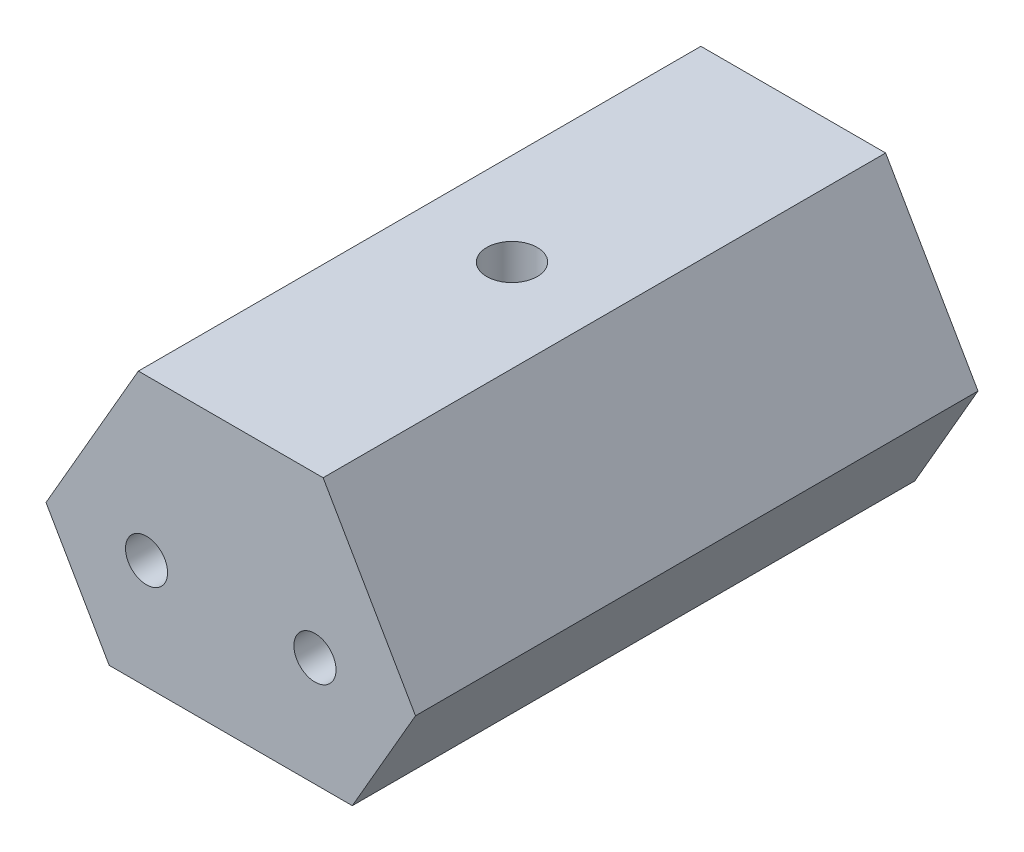
SolidWorks part; units mm, degrees
material "6061-T6 (SS)"
ref_plane "Front Plane" through (0, 0, 0) normal (0, 0, 1) x (1, 0, 0)
ref_plane "Top Plane" through (0, 0, 0) normal (0, 1, 0) x (1, 0, 0)
ref_plane "Right Plane" through (0, 0, 0) normal (1, 0, 0) x (0, 0, -1)
sketch "Sketch1" plane through (0, 0, 0) normal (0, 0, 1) x (1, 0, 0)
  line L0 (-7.2169, -6.5) -> (7.2169, -6.5)
  line L1 (-5.4848, -9.5) -> (5.4848, -9.5) construction
  line L2 (7.2169, -6.5) -> (10.9697, 0)
  line L3 (10.9697, 0) -> (5.4848, 9.5)
  line L4 (5.4848, 9.5) -> (-5.4848, 9.5)
  line L5 (-5.4848, 9.5) -> (-10.9697, 0)
  line L6 (-10.9697, 0) -> (-7.2169, -6.5)
  line L7 (-7.2169, -6.5) -> (-5.4848, -9.5) construction
  line L8 (7.2169, -6.5) -> (5.4848, -9.5) construction
  circle A0 centre (0, 0) radius 9.5 construction
  circle A1 centre (-5, 0) radius 1.25
  circle A2 centre (-5, 0) radius 1.5 construction
  circle A3 centre (5, 0) radius 1.25
  circle A4 centre (5, 0) radius 1.5 construction
  point P20 (0, 0)
  dimension "D1" = 2.5
  dimension "D2" = 3
  dimension "D3" = 2
  dimension "D6" = 3
  dimension "D4" = 19
  dimension "D5" = 10
  dimension "D7" = 3.4641
  dimension "D8" = 3.4641
extrude "Boss-Extrude1" add sketch "Sketch1" along normal mid plane 33.4
hole_wizard "1/4-28 Tapped Hole1" positions "Sketch2" profile "Sketch3" tap size "1/4-28" standard "ANSI Inch" end condition up to next
sketch "Sketch2" plane through (0, 9.5, 0) normal (0, 1, 0) x (1, 0, 0)
  point P0 (0, 0)
  point P3 (0, 0)
cosmetic thread "Hole Thread1" parameters "D2"=3.9398
sketch "Sketch3" plane through (0, 9.5, 0) normal (1, 0, 0) x (0, 0, 1)
  line L0 (0, 0) -> (0, 16)
  line L1 (0, 16) -> (1.5, 16)
  line L2 (1.5, 16) -> (1.5, 0)
  line L5 (1.5, 0) -> (0, 0)
  line L11 (0, -6.35) -> (0, 107.95) construction
  dimension "Thru Tap Drill Dia." = 3
  dimension "Thru Tap Drill Depth" = 16
